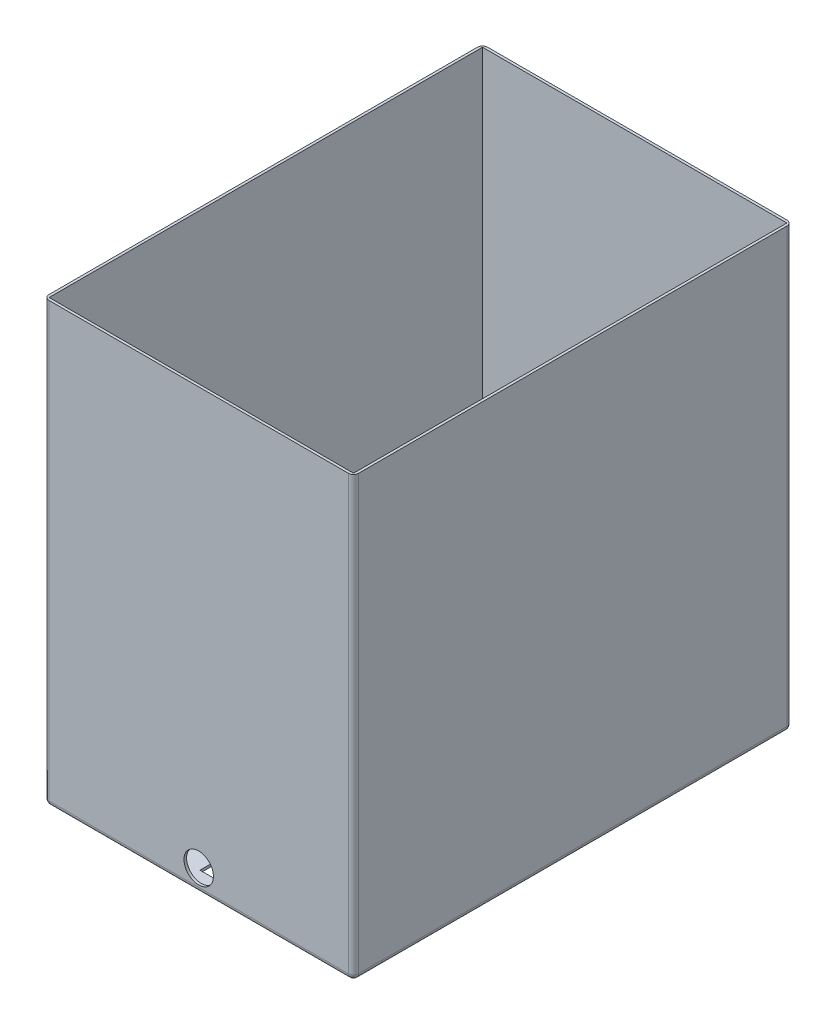
SolidWorks part; units mm, degrees
ref_plane "Front Plane" through (0, 0, 0) normal (0, 0, 1) x (1, 0, 0)
ref_plane "Top Plane" through (0, 0, 0) normal (0, 1, 0) x (1, 0, 0)
ref_plane "Right Plane" through (0, 0, 0) normal (1, 0, 0) x (0, 0, -1)
sketch "Sketch1" plane through (0, 0, 0) normal (0, 0, 1) x (1, 0, 0)
  line L1 (0, 0) -> (304.8, 0)
  line L2 (0, 0) -> (0, 431.8)
  line L4 (304.8, 0) -> (304.8, 431.8)
  line L8 (0, 431.8) -> (304.8, 431.8)
  dimension "D4" = 304.8
  dimension "D5" = 431.8
extrude "Boss-Extrude1" add sketch "Sketch1" along normal blind 431.8
sketch "Sketch2" plane through (0, 431.8, 0) normal (0, 1, 0) x (1, 0, 0)
  line L14 (2.54, -429.26) -> (302.26, -429.26)
  line L15 (302.26, -429.26) -> (302.26, -2.54)
  line L16 (302.26, -2.54) -> (2.54, -2.54)
  line L17 (2.54, -2.54) -> (2.54, -429.26)
  line L18 (2.54, -429.26) -> (302.26, -429.26)
  line L19 (302.26, -429.26) -> (302.26, -2.54)
  line L20 (302.26, -2.54) -> (2.54, -2.54)
  line L21 (2.54, -2.54) -> (2.54, -429.26)
  dimension "D1" = 2.54
extrude "Cut-Extrude1" cut sketch "Sketch2" against normal offset from surface (429.26 mm away) 2.54 contours L20 L21 L18 L19 up to face at (152.4, 0, 215.9)
fillet "Fillet1" radius 5.08 8 edges at (0, 0, 215.9) (152.4, 0, 431.8) (304.8, 0, 215.9) (152.4, 0, 0) (0, 215.9, 0) (304.8, 215.9, 0) (304.8, 215.9, 431.8) (0, 215.9, 431.8)
sketch "Sketch3" plane through (0, 2.54, 0) normal (0, 1, 0) x (1, 0, 0)
  line L0 (0, -426.72) -> (0, -5.08) construction
  line L1 (135.89, -414.02) -> (168.91, -414.02)
  line L2 (135.89, -414.02) -> (135.89, -327.914)
  line L3 (135.89, -327.914) -> (168.91, -327.914)
  line L4 (168.91, -414.02) -> (168.91, -327.914)
  line L8 (299.72, -431.8) -> (5.08, -431.8) construction
  dimension "D1" = 86.106
  dimension "D2" = 33.02
  dimension "D3" = 17.78
  dimension "D4" = 135.89
extrude "Cut-Extrude2" cut sketch "Sketch3" against normal through all
sketch "Sketch10" plane through (0, 0, 431.8) normal (0, 0, 1) x (1, 0, 0)
  line L0 (299.72, 0) -> (5.08, 0) construction
  line L1 (0, 5.08) -> (0, 431.8) construction
  circle A0 centre (152.4, 21.59) radius 14.478
  dimension "D1" = 28.956
  dimension "D2" = 21.59
  dimension "D3" = 152.4
extrude "Cut-Extrude7" cut sketch "Sketch10" against normal blind 7.62
ref_plane "Plane1" through (152.4, 0, 0) normal (-1, 0, 0) x (0, 0, 1)
